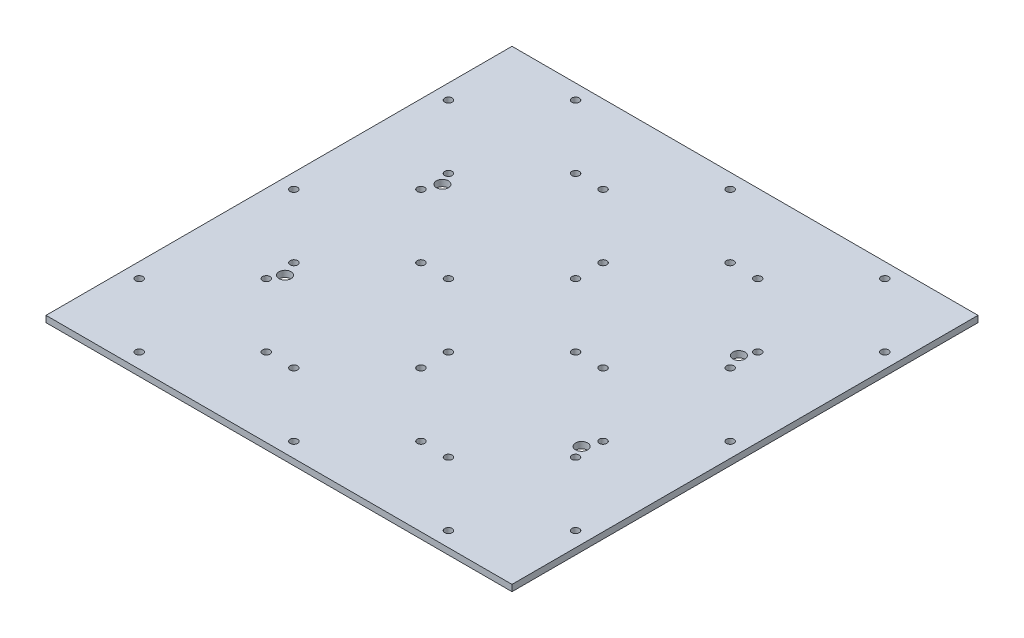
SolidWorks part; units mm, degrees
ref_plane "Front Plane" through (0, 0, 0) normal (0, 0, 1) x (1, 0, 0)
ref_plane "Top Plane" through (0, 0, 0) normal (0, 1, 0) x (1, 0, 0)
ref_plane "Right Plane" through (0, 0, 0) normal (1, 0, 0) x (0, 0, -1)
sketch "Sketch1" plane through (0, 0, 0) normal (0, 1, 0) x (1, 0, 0)
  line L1 (110, -110) -> (-110, -110)
  line L2 (110, -110) -> (110, 110)
  line L3 (110, 110) -> (-110, 110)
  line L4 (-110, -110) -> (-110, 110)
  line L5 (110, -110) -> (-110, 110) construction
  line L6 (110, 110) -> (-110, -110) construction
  point P0 (0, 0)
  dimension "D1" = 220
  dimension "D2" = 220
extrude "Boss-Extrude1" add sketch "Sketch1" along normal blind 3
sketch "Sketch2" plane through (0, 3, 0) normal (0, 1, 0) x (1, 0, 0)
  line L0 (-110, 103) -> (110, 103) construction
  line L1 (-110, 110) -> (-110, -110) construction
  line L2 (110, -110) -> (110, 110) construction
  line L3 (110, 110) -> (-110, 110) construction
  line L4 (0, 110) -> (0, -110) construction
  line L5 (-110, -110) -> (110, -110) construction
  line L9 (-110, 0) -> (110, 0) construction
  line L10 (-73, 103) -> (-73, 43) construction
  circle A0 centre (-73, 103) radius 1.7526
  circle A1 centre (0, 103) radius 1.7526
  circle A2 centre (-30, 73) radius 1.7526
  circle A3 centre (-103, 73) radius 1.7526
  circle A4 centre (-43, 73) radius 1.7526
  circle A5 centre (0, 43) radius 1.7526
  circle A6 centre (30, 73) radius 1.7526
  circle A7 centre (73, 103) radius 1.7526
  circle A8 centre (43, 73) radius 1.7526
  circle A9 centre (-73, 43) radius 1.7526
  circle A10 centre (73, 43) radius 1.7526
  circle A11 centre (103, 73) radius 1.7526
  circle A12 centre (0, 30) radius 1.7526
  circle A13 centre (-30, 0) radius 1.7526
  circle A14 centre (0, -30) radius 1.7526
  circle A15 centre (30, 0) radius 1.7526
  circle A16 centre (73, 30) radius 1.7526
  circle A17 centre (43, 0) radius 1.7526
  circle A18 centre (73, -30) radius 1.7526
  circle A19 centre (103, 0) radius 1.7526
  circle A20 centre (0, -43) radius 1.7526
  circle A21 centre (-30, -73) radius 1.7526
  circle A22 centre (0, -103) radius 1.7526
  circle A23 centre (30, -73) radius 1.7526
  circle A24 centre (73, -43) radius 1.7526
  circle A25 centre (43, -73) radius 1.7526
  circle A26 centre (73, -103) radius 1.7526
  circle A27 centre (103, -73) radius 1.7526
  circle A28 centre (-73, 30) radius 1.7526
  circle A29 centre (-103, 0) radius 1.7526
  circle A30 centre (-73, -30) radius 1.7526
  circle A31 centre (-43, 0) radius 1.7526
  circle A32 centre (-73, -43) radius 1.7526
  circle A33 centre (-103, -73) radius 1.7526
  circle A34 centre (-73, -103) radius 1.7526
  circle A35 centre (-43, -73) radius 1.7526
  circle A36 centre (-73, 73) radius 30 construction
  point P64 (0, 0)
  point P95 (-73, 73)
  dimension "D2" = 3.5052
  dimension "D4" = 60
  dimension "D5" = 3
  dimension "D1" = 7
  dimension "D3" = 3
  dimension "D6" = 7
sketch "Sketch3" plane through (0, 3, 0) normal (0, 1, 0) x (1, 0, 0)
  line L1 (-110, 110) -> (-110, -110) construction
  line L2 (110, -110) -> (110, 110) construction
  line L3 (110, 110) -> (-110, 110) construction
  line L4 (0, 110) -> (0, -110) construction
  line L5 (-110, -110) -> (110, -110) construction
  line L6 (-110, 0) -> (110, 0) construction
  line L7 (70, 110) -> (70, -110) construction
  circle A0 centre (70, -37.15) radius 2.85
  circle A1 centre (-70, -37.15) radius 2.85
  circle A2 centre (-70, 37.15) radius 2.85
  circle A4 centre (70, 37.15) radius 2.85
  dimension "D1" = 5.7
  dimension "D5" = 72.85
  dimension "D4" = 40
extrude "Cut-Extrude5" cut sketch "Sketch3" against normal through all
extrude "Cut-Extrude6" cut sketch "Sketch2" against normal through all
